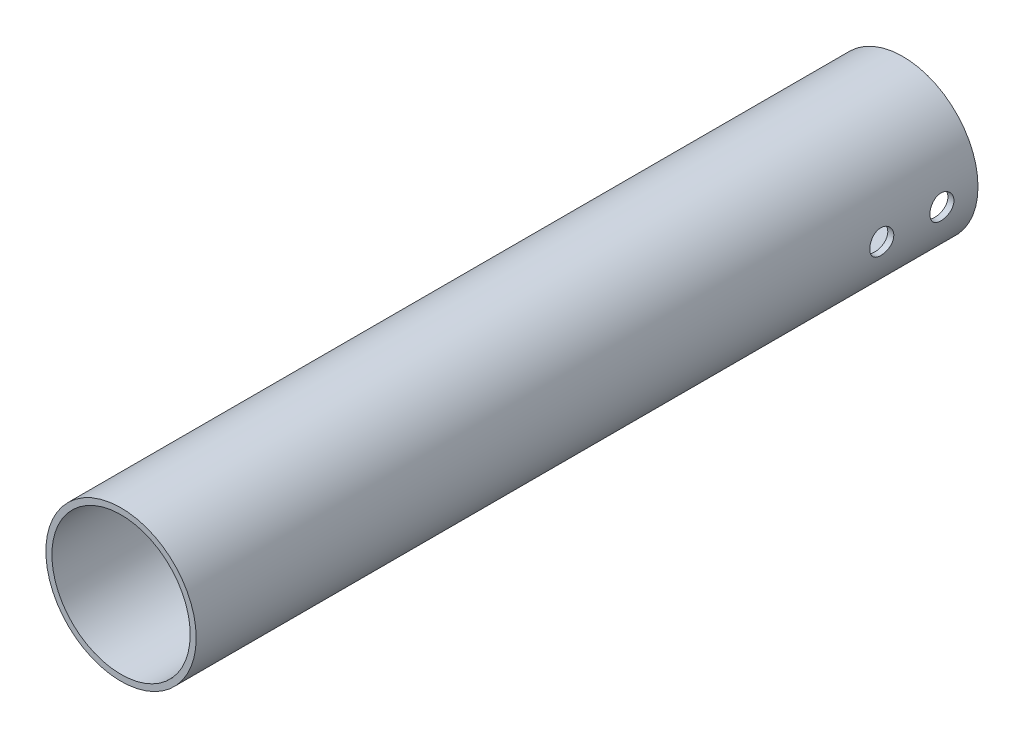
SolidWorks part; units mm, degrees
material "Hexcel AS4C (3000 Filaments)"
ref_plane "Front Plane" through (0, 0, 0) normal (0, 0, 1) x (1, 0, 0)
ref_plane "Top Plane" through (0, 0, 0) normal (0, 1, 0) x (1, 0, 0)
ref_plane "Right Plane" through (0, 0, 0) normal (1, 0, 0) x (0, 0, -1)
sketch "Sketch1" plane through (0, 0, 0) normal (0, 0, 1) x (1, 0, 0)
  circle A0 centre (0, 0) radius 11.5
  circle A1 centre (0, 0) radius 12.5
  dimension "D1" = 23
  dimension "D2" = 25
extrude "Boss-Extrude1" add sketch "Sketch1" along normal blind 130
sketch "Sketch2" plane through (0, 0, 0) normal (1, 0, 0) x (0, 0, -1)
  line L0 (0, -12.5) -> (0, 12.5) construction
  circle A0 centre (-6, 0) radius 2
  circle A1 centre (-16, 0) radius 2
  dimension "D1" = 4
  dimension "D2" = 4
  dimension "D3" = 10
  dimension "D4" = 6
extrude "Cut-Extrude1" cut sketch "Sketch2" against normal through all both and the other way through all
